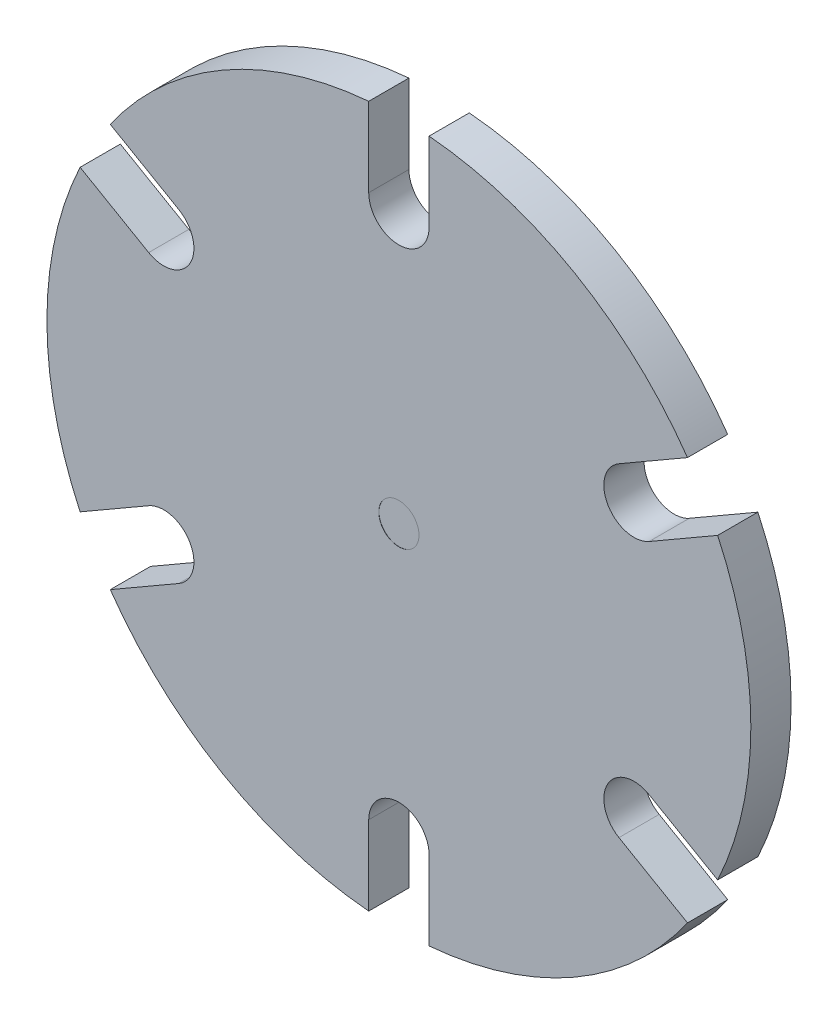
SolidWorks part; units mm, degrees
ref_plane "Front Plane" through (0, 0, 0) normal (0, 0, 1) x (1, 0, 0)
ref_plane "Top Plane" through (0, 0, 0) normal (0, 1, 0) x (1, 0, 0)
ref_plane "Right Plane" through (0, 0, 0) normal (1, 0, 0) x (0, 0, -1)
sketch "Sketch1" plane through (0, 0, 0) normal (0, 0, 1) x (1, 0, 0)
  circle A0 centre (0, 0) radius 17.5
  dimension "D1" = 35
extrude "Boss-Extrude1" add sketch "Sketch1" along normal blind 2
sketch "Sketch2" plane through (0, 0, 0) normal (0, 0, -1) x (-1, 0, 0)
  circle A0 centre (0, 0) radius 10
  dimension "D1" = 20
extrude "Boss-Extrude2" add sketch "Sketch2" along normal blind 1
sketch "Sketch4" plane through (0, 0, 2) normal (0, 0, 1) x (1, 0, 0)
  line L0 (-5.2568, 13.5) -> (4.886, 13.5) construction
  line L1 (-2.6671, 17.5) -> (2.8706, 17.5) construction
  line L4 (-1.5, 13.5) -> (-1.5, 17.5)
  line L5 (-1.5, 17.5) -> (1.5, 17.5)
  line L6 (1.5, 13.5) -> (1.5, 17.5)
  circle A0 centre (0, 0) radius 17.5 construction
  arc A1 (-1.5, 13.5) -> (1.5, 13.5) centre (0, 13.5) ccw
  point P2 (0, 17.5)
  dimension "D2" = 3
  dimension "D1" = 4
extrude "Cut-Extrude1" cut sketch "Sketch4" against normal blind 6
sketch "Sketch5" plane through (0, 0, 2) normal (0, 0, 1) x (1, 0, 0)
  circle A0 centre (0, 0) radius 1
extrude "Cut-Extrude2" cut sketch "Sketch5" against normal blind 0.01
pattern_circular "CirPattern1" count 6 over 360 about axis through (0, 0, 0) along (0, 0, 1) of "Cut-Extrude1"
fillet "Fillet1" radius 0.3 1 edges at (-10, 0, -1)
